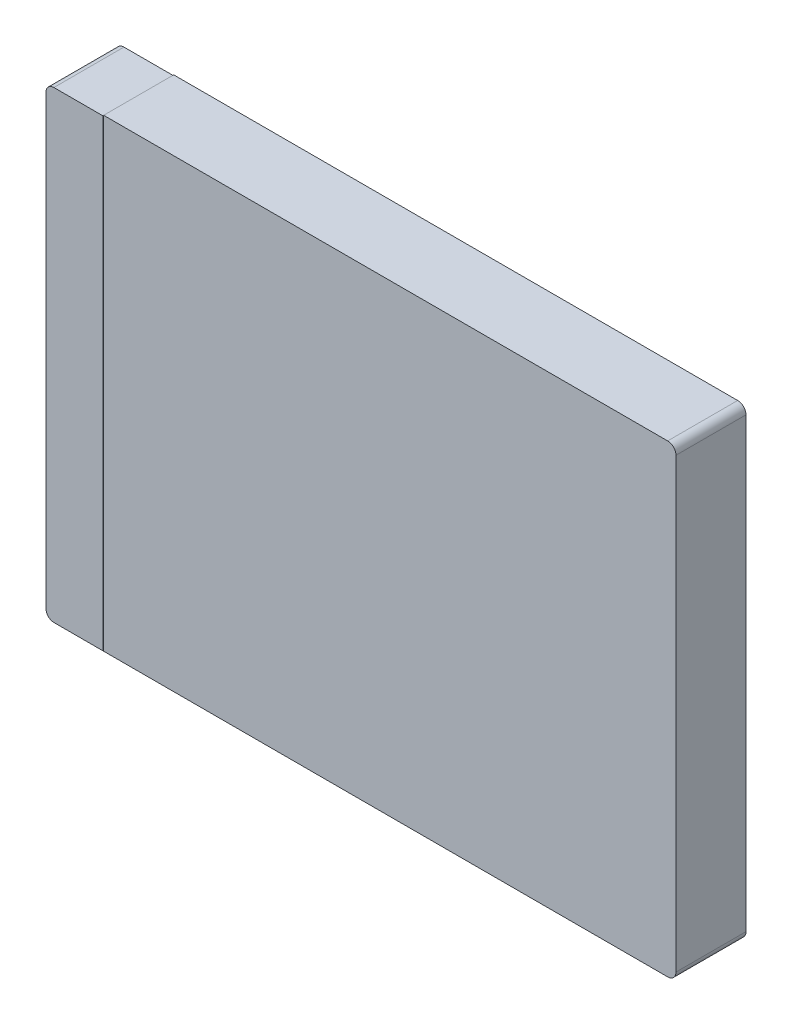
SolidWorks part; units mm, degrees
ref_plane "Front Plane" through (0, 0, 0) normal (0, 0, 1) x (1, 0, 0)
ref_plane "Top Plane" through (0, 0, 0) normal (0, 1, 0) x (1, 0, 0)
ref_plane "Right Plane" through (0, 0, 0) normal (1, 0, 0) x (0, 0, -1)
sketch "Sketch1" plane through (0, 0, 0) normal (0, 0, 1) x (1, 0, 0)
  line L1 (-31.041, -0.2149) -> (7.567, -0.2149)
  line L2 (-31.041, -0.2149) -> (-31.041, -28.6629)
  line L3 (-31.041, -28.6629) -> (7.567, -28.6629)
  line L4 (7.567, -0.2149) -> (7.567, -28.6629)
  dimension "D1" = 28.448
  dimension "D2" = 38.608
extrude "Boss-Extrude1" add sketch "Sketch1" along normal blind 4.318
fillet "Fillet1" radius 0.508 4 edges at (7.567, -0.2149, 2.159) (7.567, -28.6629, 2.159) (-31.041, -28.6629, 2.159) (-31.041, -0.2149, 2.159)
sketch "Sketch2" plane through (0, 0, 0) normal (0, 0, -1) x (-1, 0, 0)
  line L5 (-12.5446, 6.3377) -> (27.5082, 6.3377)
  line L6 (-12.5446, 6.3377) -> (-12.5446, -32.1285)
  line L7 (-12.5446, -32.1285) -> (27.5082, -32.1285)
  line L8 (30.533, -0.2403) -> (-7.059, -0.2403)
  line L9 (-7.5416, -0.7229) -> (-7.5416, -28.1549)
  line L10 (-7.059, -28.6375) -> (30.533, -28.6375)
  line L11 (31.0156, -28.1549) -> (31.0156, -0.7229)
  line L12 (30.533, -0.2403) -> (-7.059, -0.2403)
  line L13 (-7.5416, -0.7229) -> (-7.5416, -28.1549)
  line L14 (-7.059, -28.6375) -> (30.533, -28.6375)
  line L15 (31.0156, -28.1549) -> (31.0156, -0.7229)
  line L16 (27.5082, 6.3377) -> (27.5082, -32.1285)
  arc A8 (-7.059, -0.2403) -> (-7.5416, -0.7229) centre (-7.059, -0.7229) ccw
  arc A9 (-7.5416, -28.1549) -> (-7.059, -28.6375) centre (-7.059, -28.1549) ccw
  arc A10 (30.533, -28.6375) -> (31.0156, -28.1549) centre (30.533, -28.1549) ccw
  arc A11 (31.0156, -0.7229) -> (30.533, -0.2403) centre (30.533, -0.7229) ccw
  arc A12 (-7.059, -0.2403) -> (-7.5416, -0.7229) centre (-7.059, -0.7229) ccw
  arc A13 (-7.5416, -28.1549) -> (-7.059, -28.6375) centre (-7.059, -28.1549) ccw
  arc A14 (30.533, -28.6375) -> (31.0156, -28.1549) centre (30.533, -28.1549) ccw
  arc A15 (31.0156, -0.7229) -> (30.533, -0.2403) centre (30.533, -0.7229) ccw
  dimension "D1" = 0.0254
extrude "Cut-Extrude1" cut sketch "Sketch2" against normal blind 0.0254 contours L15 A15 L12 L16 L14 A14
sketch "Sketch3" plane through (0, 0, 0) normal (0, 0, -1) x (-1, 0, 0)
  line L1 (-12.5446, 6.3377) -> (27.5082, 6.3377)
  line L2 (-12.5446, 6.3377) -> (-12.5446, -32.1285)
  line L3 (-12.5446, -32.1285) -> (27.5082, -32.1285)
  line L4 (27.5082, 6.3377) -> (27.5082, -32.1285)
  arc M5 (30.533, -0.2403) -> (31.0156, -0.7229) centre (30.533, -0.7229) cw
  line M6 (31.0156, -0.7229) -> (31.0156, -28.1549)
  arc M7 (31.0156, -28.1549) -> (30.533, -28.6375) centre (30.533, -28.1549) cw
  line M8 (30.533, -28.6375) -> (27.5082, -28.6375)
  line M10 (27.5082, -0.2403) -> (30.533, -0.2403)
  line M11 (30.533, -0.2149) -> (-7.059, -0.2149)
  line M15 (-7.059, -28.6629) -> (30.533, -28.6629)
  arc M16 (30.533, -28.6629) -> (31.041, -28.1549) centre (30.533, -28.1549) ccw
  line M17 (31.041, -28.1549) -> (31.041, -0.7229)
  arc M18 (31.041, -0.7229) -> (30.533, -0.2149) centre (30.533, -0.7229) ccw
extrude "Cut-Extrude2" cut sketch "Sketch3" against normal through all contours L4 M11 M10 M5 M6 M7 M8 M15 M16 M17 M18
sketch "Sketch4" plane through (0, 0, 4.318) normal (0, 0, 1) x (1, 0, 0)
  line L1 (-27.5082, 6.3377) -> (12.5446, 6.3377)
  line L2 (-27.5082, 6.3377) -> (-27.5082, -32.1285)
  line L3 (-27.5082, -32.1285) -> (12.5446, -32.1285)
  line L4 (12.5446, 6.3377) -> (12.5446, -32.1285)
extrude "Cut-Extrude3" cut sketch "Sketch4" against normal blind 0.0254
